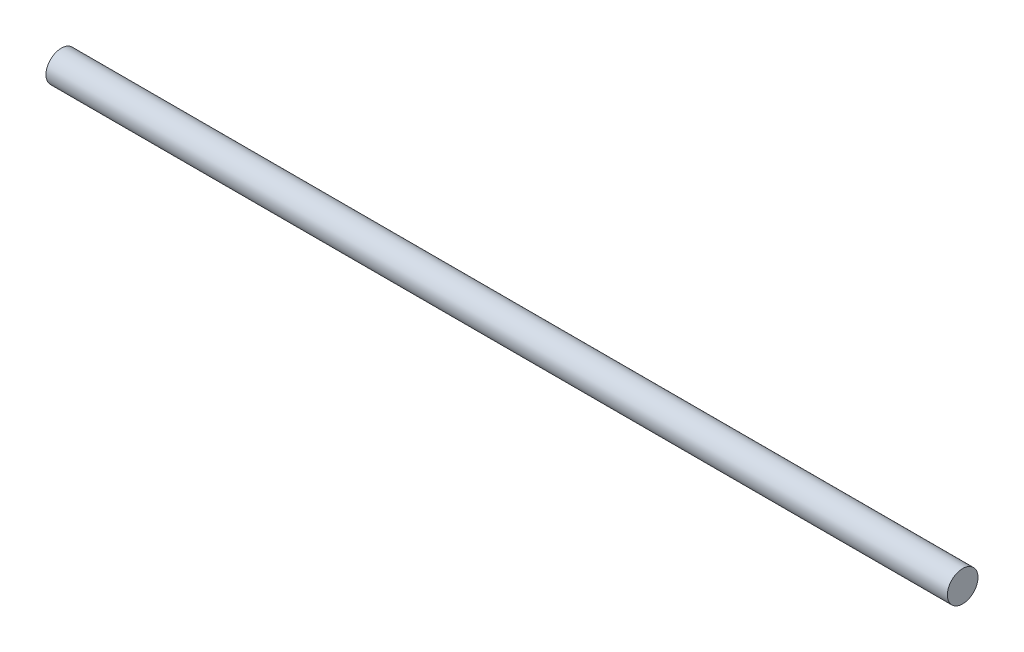
SolidWorks part; units mm, degrees
ref_plane "Alzado" through (0, 0, 0) normal (0, 0, 1) x (1, 0, 0)
ref_plane "Planta" through (0, 0, 0) normal (0, 1, 0) x (1, 0, 0)
ref_plane "Vista lateral" through (0, 0, 0) normal (1, 0, 0) x (0, 0, -1)
sketch "Croquis1" plane through (0, 0, 0) normal (1, 0, 0) x (0, 0, -1)
  circle A0 centre (0, 0) radius 0.85
  dimension "D1" = 1.7
extrude "Saliente-Extruir1" add sketch "Croquis1" along normal mid plane 50
